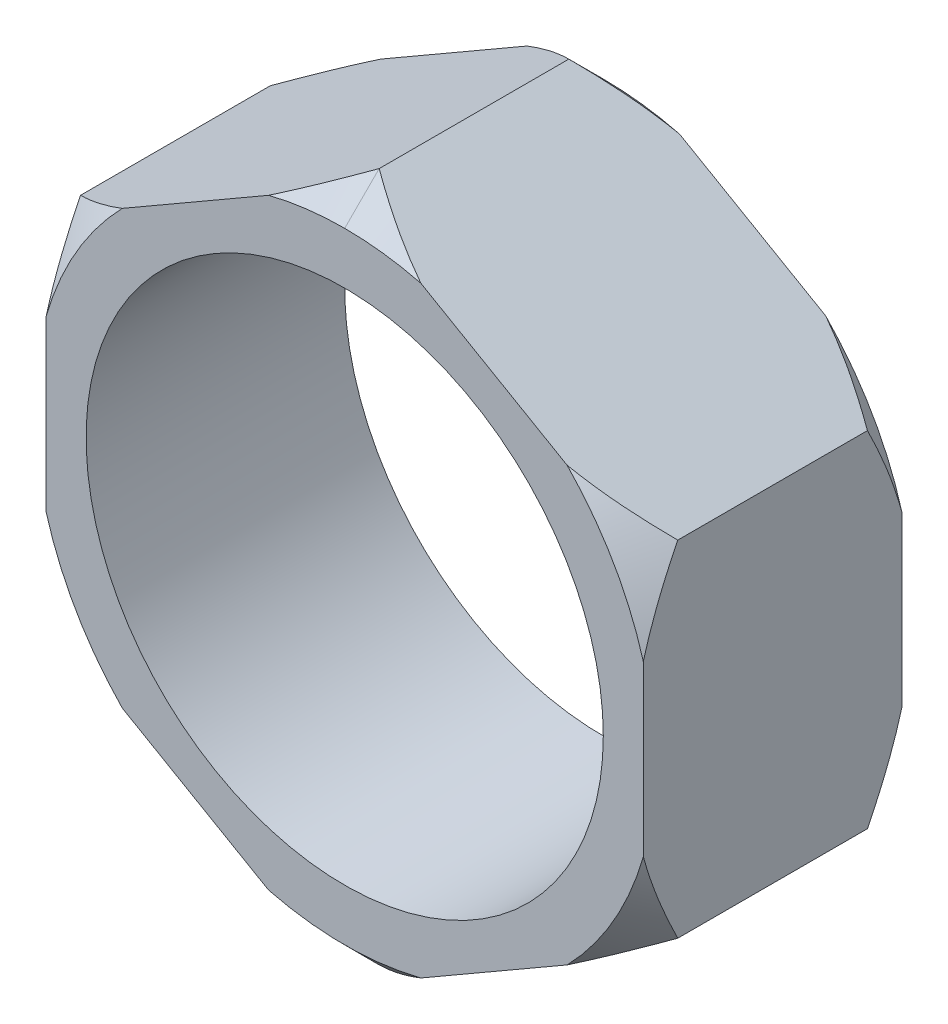
SolidWorks part; units mm, degrees
material "普通碳钢"
ref_plane "Front" through (0, 0, 0) normal (0, 0, 1) x (1, 0, 0)
ref_plane "Top" through (0, 0, 0) normal (0, 1, 0) x (1, 0, 0)
ref_plane "Right" through (0, 0, 0) normal (1, 0, 0) x (0, 0, -1)
sketch "草图2" plane through (0, 0, 0) normal (0, 0, 1) x (1, 0, 0)
  line L15 (-1.7321, 1) -> (-1.7321, -1)
  line L16 (-1.7321, -1) -> (0, -2)
  line L17 (0, -2) -> (1.7321, -1)
  line L18 (1.7321, -1) -> (1.7321, 1)
  line L19 (1.7321, 1) -> (0, 2)
  line L20 (0, 2) -> (-1.7321, 1)
  circle A1 centre (0, 0) radius 1.7321 construction
extrude "凸台-拉伸1" add sketch "草图2" along normal blind 1.5
sketch "草图3" plane through (0, 0, 1.5) normal (0, 0, 1) x (1, 0, 0)
  circle A0 centre (0, 0) radius 1.5
extrude "切除-拉伸1" cut sketch "草图3" against normal blind 1.5 contours A0
cosmetic thread "装饰螺纹线1" parameters "D2"=4
sketch "草图4" plane through (0, 0, 0) normal (0, 0, -1) x (-1, 0, 0)
  circle A0 centre (0, 0) radius 1.8
sketch "草图5" plane through (0, 0, 0) normal (1, 0, 0) x (0, 0, -1)
  line L0 (0, 2) -> (-0.2, 2)
  line L1 (-1.5, 2) -> (0, 2) construction
  line L2 (-0.2, 2) -> (0, 1.8)
  line L3 (0, -1.8) -> (0, 1.8) construction
  line L4 (0, 1.8) -> (0, 2)
  line L5 (-1.5, 2) -> (-1.3, 2)
  line L6 (-1.3, 2) -> (-1.5, 1.8)
  line L7 (-1.5, 1) -> (-1.5, 2) construction
  line L8 (-1.5, 1.8) -> (-1.5, 2)
  dimension "D1" = 0.2
sweep "切除-扫描4" cut profiles "草图5" path "草图4"
